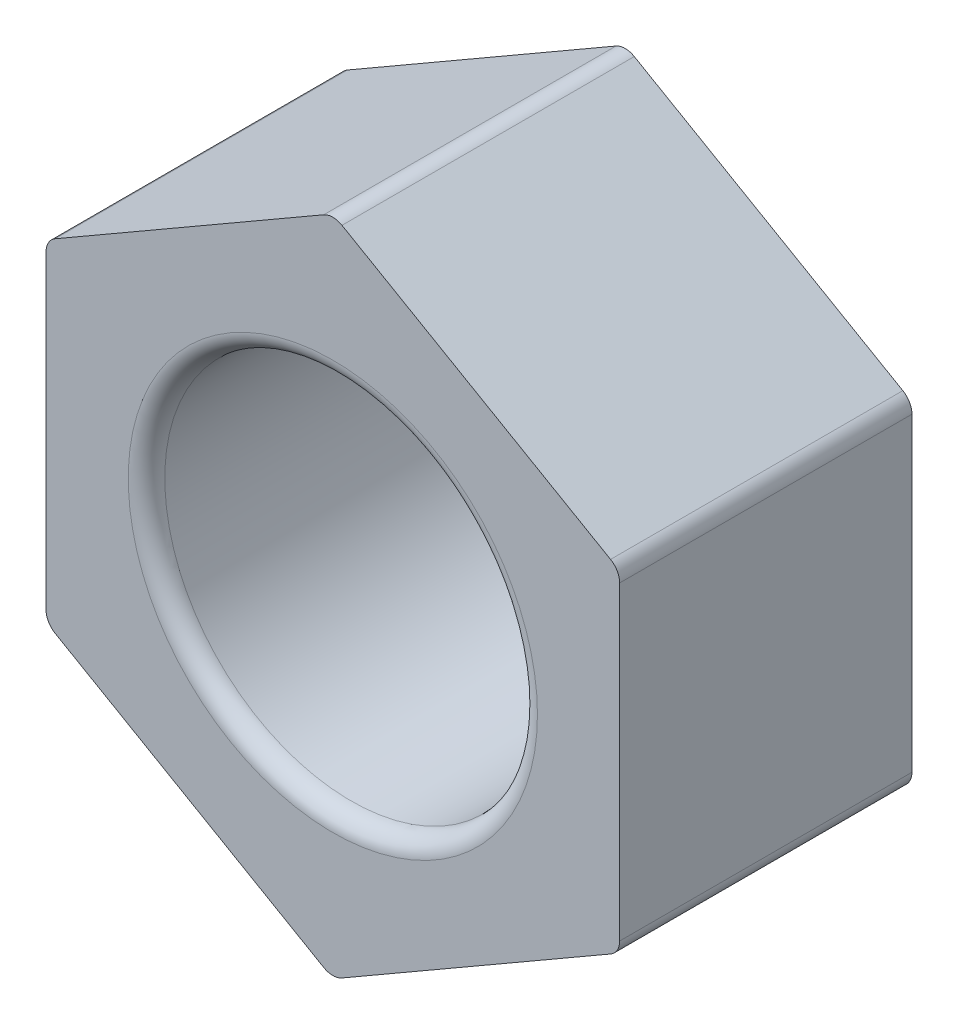
SolidWorks part; units mm, degrees
ref_plane "Front Plane" through (0, 0, 0) normal (0, 0, 1) x (1, 0, 0)
ref_plane "Top Plane" through (0, 0, 0) normal (0, 1, 0) x (1, 0, 0)
ref_plane "Right Plane" through (0, 0, 0) normal (1, 0, 0) x (0, 0, -1)
sketch "Sketch1" plane through (0, 0, 0) normal (0, 0, 1) x (1, 0, 0)
  line L1 (0, 4.5322) -> (-3.925, 2.2661)
  line L2 (-3.925, 2.2661) -> (-3.925, -2.2661)
  line L3 (-3.925, -2.2661) -> (0, -4.5322)
  line L4 (0, -4.5322) -> (3.925, -2.2661)
  line L5 (3.925, -2.2661) -> (3.925, 2.2661)
  line L6 (3.925, 2.2661) -> (0, 4.5322)
  circle A0 centre (0, 0) radius 3.925 construction
  dimension "D1" = 7.85
extrude "Boss-Extrude1" add sketch "Sketch1" along normal blind 4
sketch "Sketch2" plane through (0, 0, 4) normal (0, 0, 1) x (1, 0, 0)
  circle A0 centre (0, 0) radius 2.55
  dimension "D1" = 5.1
extrude "Cut-Extrude1" cut sketch "Sketch2" against normal through all
fillet "Fillet1" radius 0.25 8 edges at (2.55, 0, 4) (2.55, 0, 0) (-3.925, 2.2661, 2) (-3.925, -2.2661, 2) (0, -4.5322, 2) (3.925, -2.2661, 2) (3.925, 2.2661, 2) (0, 4.5322, 2)
